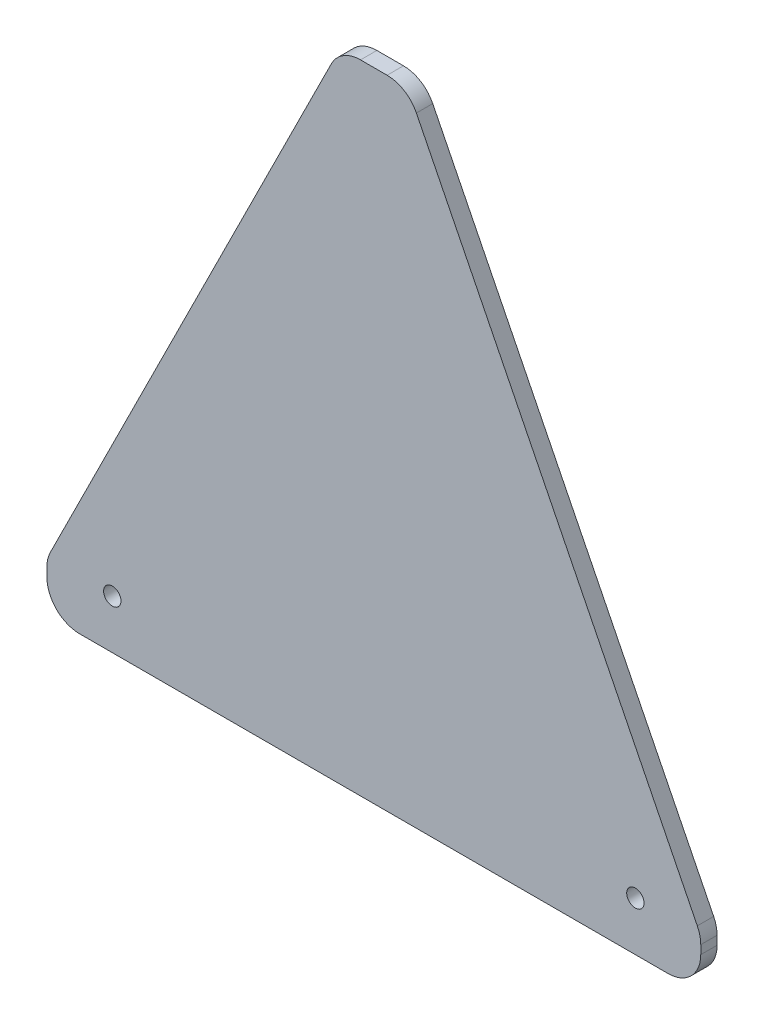
SolidWorks part; units mm, degrees
material "PE High Density"
ref_plane "Front Plane" through (0, 0, 0) normal (0, 0, 1) x (1, 0, 0)
ref_plane "Top Plane" through (0, 0, 0) normal (0, 1, 0) x (1, 0, 0)
ref_plane "Right Plane" through (0, 0, 0) normal (1, 0, 0) x (0, 0, -1)
sketch "Sketch1" plane through (0, 0, 0) normal (0, 0, 1) x (1, 0, 0)
  line L7 (0, 19.05) -> (127, 273.7726) construction
  line L24 (0, 0) -> (254, 0)
  line L25 (0, 0) -> (0, 19.05)
  line L26 (0, 19.05) -> (254, 19.05) construction
  line L27 (254, 0) -> (254, 19.05)
  line L28 (127, 273.7726) -> (254, 19.05) construction
  line L29 (113.9758, 247.65) -> (140.0242, 247.65)
  line L30 (0, 19.05) -> (113.9758, 247.65)
  line L31 (140.0242, 247.65) -> (254, 19.05)
  circle A6 centre (25.4, 19.05) radius 3.3734
  circle A7 centre (228.6, 19.05) radius 3.3734
  point P7 (127, 0)
  dimension "D3" = 63.5
  dimension "D6" = 19.05
  dimension "D5" = 203.2
  dimension "D7" = 6.7469
  dimension "D1" = 254
  dimension "D2" = 19.05
  dimension "D4" = 25.4
  dimension "D8" = 228.6
extrude "Boss-Extrude1" add sketch "Sketch1" along normal blind 6.35
fillet "Fillet2" radius 12.7 6 edges at (113.9758, 247.65, 3.175) (140.0242, 247.65, 3.175) (254, 19.05, 3.175) (254, 0, 3.175) (0, 0, 3.175) (0, 19.05, 3.175)
